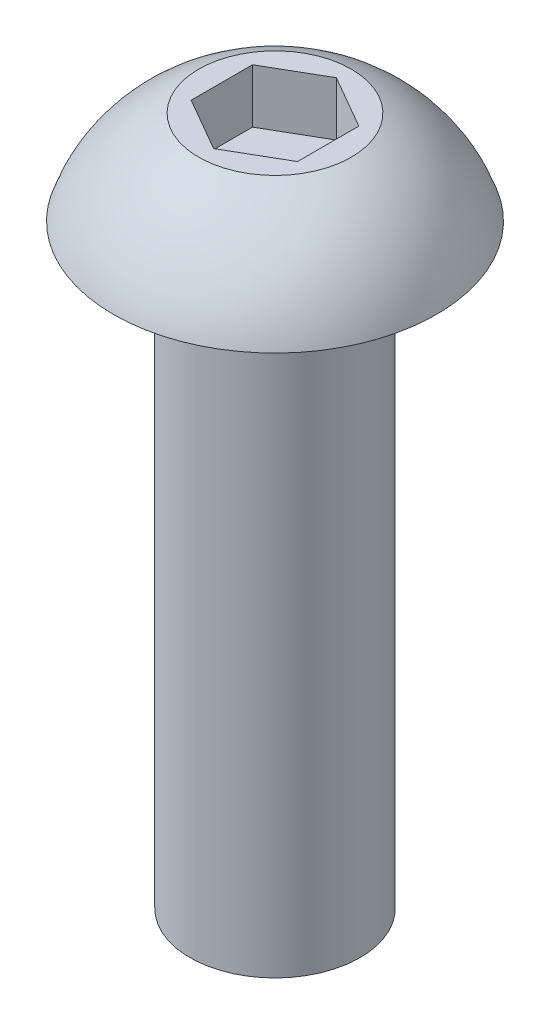
SolidWorks part; units mm, degrees
material "AISI Type 316L stainless steel"
ref_plane "Front Plane" through (0, 0, 0) normal (0, 0, 1) x (1, 0, 0)
ref_plane "Top Plane" through (0, 0, 0) normal (0, 1, 0) x (1, 0, 0)
ref_plane "Right Plane" through (0, 0, 0) normal (1, 0, 0) x (0, 0, -1)
sketch "Sketch1" plane through (0, 0, 0) normal (0, 0, 1) x (1, 0, 0)
  line L0 (-2, 0) -> (-3.8, 0)
  line L1 (-2, 0) -> (-2, -14)
  line L2 (0, -14) -> (0, 2.2)
  line L3 (0, 2.2) -> (-1.7948, 2.2)
  line L4 (-2, -14) -> (0, -14)
  arc A0 (-3.8, 0) -> (-1.7948, 2.2) centre (-0.4063, -1.0794) cw
  dimension "D1" = 14
  dimension "D2" = 2.2
  dimension "D3" = 3.8
  dimension "D4" = 2
  dimension "D5" = 1.7948
revolve "Revolve1" add sketch "Sketch1" angle 360 about L2
sketch "Sketch2" plane through (0, 2.2, 0) normal (0, 1, 0) x (1, 0, 0)
  line L0 (0, 0) -> (0, 1.4434) construction
  line L1 (-1.25, 0.7217) -> (-1.25, -0.7217)
  line L2 (-1.25, -0.7217) -> (0, -1.4434)
  line L3 (0, -1.4434) -> (1.25, -0.7217)
  line L4 (1.25, -0.7217) -> (1.25, 0.7217)
  line L5 (1.25, 0.7217) -> (0, 1.4434)
  line L6 (0, 1.4434) -> (-1.25, 0.7217)
  circle A0 centre (0, 0) radius 1.25 construction
  dimension "D1" = 2.5
extrude "Cut-Extrude1" cut sketch "Sketch2" against normal blind 1.27
